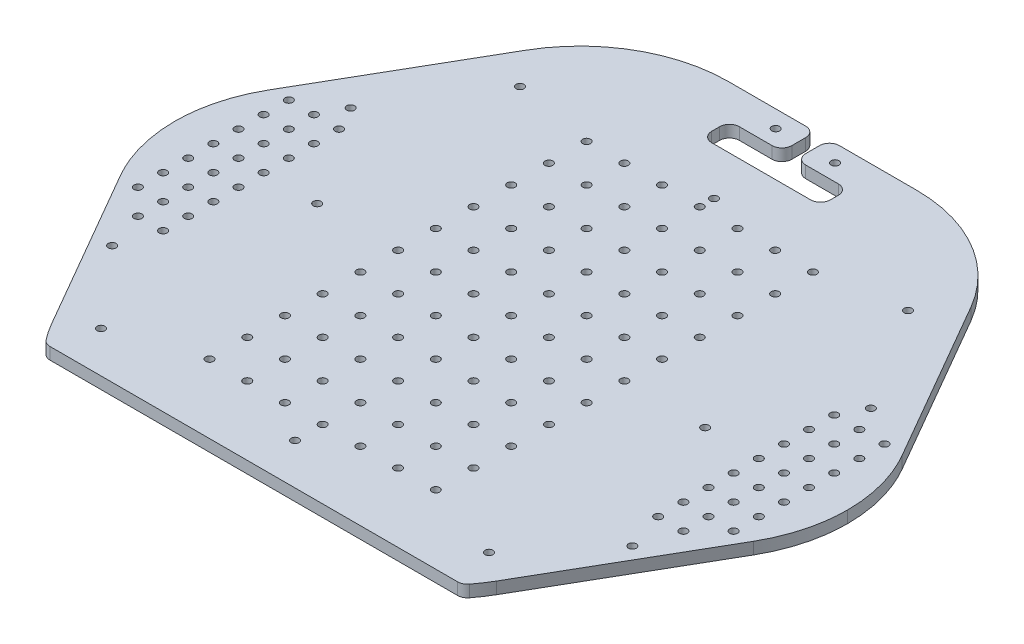
SolidWorks part; units mm, degrees
ref_plane "Front Plane" through (0, 0, 0) normal (0, 0, 1) x (1, 0, 0)
ref_plane "Top Plane" through (0, 0, 0) normal (0, 1, 0) x (1, 0, 0)
ref_plane "Right Plane" through (0, 0, 0) normal (1, 0, 0) x (0, 0, -1)
ref_plane "Plane1" through (0, 6, 0) normal (0, 1, 0) x (1, 0, 0)
sketch "Sketch1" plane through (0, 6, 0) normal (0, 1, 0) x (1, 0, 0)
  line L0 (112.4519, -119.7724) -> (159.9519, -37.5)
  line L1 (159.9519, 37.5) -> (90.8013, 157.2724)
  line L2 (90.8013, 157.2724) -> (-90.8013, 157.2724)
  line L3 (-90.8013, 157.2724) -> (-159.9519, 37.5)
  line L4 (-159.9519, -37.5) -> (-112.4519, -119.7724)
  line L5 (-105.3856, -130) -> (105.3856, -130)
  spline S0 degree 3 poles (105.3856, -130) (105.779, -129.4973) (106.1723, -128.9946) (106.5657, -128.4919) (108.7286, -125.7279) (110.697, -122.8118) (112.4519, -119.7724) knots 2.452075 2.452075 2.452075 2.452075 2.477608 2.477608 2.477608 2.617994 2.617994 2.617994 2.617994
  spline S1 degree 3 poles (159.9519, -37.5) (162.0898, -33.7968) (165.8426, -25.7861) (169.2445, -13.0899) (169.9999, -4.2761) (170, 0) knots 2.617994 2.617994 2.617994 2.617994 2.789036 2.97055 3.141593 3.141593 3.141593 3.141593
  spline S2 degree 3 poles (170, 0) (169.9999, 4.276) (169.2445, 13.0899) (165.8426, 25.7861) (162.0898, 33.7968) (159.9519, 37.5) knots 3.141593 3.141593 3.141593 3.141593 3.312635 3.494149 3.665191 3.665191 3.665191 3.665191
  spline S3 degree 3 poles (-159.9519, 37.5) (-162.0898, 33.7968) (-165.8426, 25.7861) (-169.2445, 13.0899) (-169.9999, 4.2761) (-170, 0) knots 5.759587 5.759587 5.759587 5.759587 5.930629 6.112143 6.283185 6.283185 6.283185 6.283185
  spline S4 degree 3 poles (-170, 0) (-169.9999, -4.2761) (-169.2445, -13.0899) (-165.8426, -25.7861) (-162.0898, -33.7968) (-159.9519, -37.5) knots 6.283185 6.283185 6.283185 6.283185 6.454228 6.635742 6.806784 6.806784 6.806784 6.806784
  spline S5 degree 3 poles (-112.4519, -119.7724) (-110.697, -122.8118) (-108.7286, -125.7279) (-106.5657, -128.4919) (-106.1723, -128.9946) (-105.779, -129.4973) (-105.3856, -130) knots 0.523599 0.523599 0.523599 0.523599 0.663985 0.663985 0.663985 0.689517 0.689517 0.689517 0.689517
extrude "Boss-Extrude1" add sketch "Sketch1" against normal blind 6
sketch "Sketch2" plane through (0, 0, 0) normal (0, -1, 0) x (1, 0, 0)
  line L0 (3.5, -157.2724) -> (3.5, -140.2724)
  line L1 (3.5, -140.2724) -> (30, -140.2724)
  line L2 (30, -140.2724) -> (30, -126.2724)
  line L3 (30, -126.2724) -> (-30, -126.2724)
  line L4 (-30, -126.2724) -> (-30, -140.2724)
  line L5 (-30, -140.2724) -> (-3.5, -140.2724)
  line L6 (-3.5, -140.2724) -> (-3.5, -157.2724)
  line L7 (-3.5, -157.2724) -> (3.5, -157.2724)
extrude "Cut-Extrude1" cut sketch "Sketch2" against normal through all
hole_wizard "M3.5 Clearance Hole1" positions "Sketch4" profile "Sketch3" hole size "M3.5" standard "ANSI Metric"
sketch "Sketch4" plane through (0, 6, 0) normal (0, 1, 0) x (1, 0, 0)
  point P0 (-150.4696, 38.1)
  point P1 (-150.4696, 25.4)
  point P2 (-150.4696, 12.7)
  point P3 (-150.4696, 0)
  point P4 (-150.4696, -12.7)
  point P5 (-150.4696, -25.4)
  point P6 (-150.4696, -38.1)
  point P7 (150.4696, -38.1)
  point P8 (150.4696, -25.4)
  point P9 (150.4696, -12.7)
  point P10 (150.4696, 0)
  point P11 (150.4696, 12.7)
  point P12 (150.4696, 25.4)
  point P13 (150.4696, 38.1)
sketch "Sketch3" plane through (-150.4696, 6, -38.1) normal (1, 0, 0) x (0, 0, 1)
  line L0 (0, 0) -> (0, 6.0001)
  line L1 (0, 6.0001) -> (1.9748, 6.0001)
  line L2 (1.9748, 6.0001) -> (1.9748, 0)
  line L5 (1.9748, 0) -> (0, 0)
  line L11 (0, -6.35) -> (0, 107.95) construction
  dimension "Thru Hole Dia." = 3.9496
  dimension "Thru Hole Depth" = 6.0001
hole_wizard "M3.5 Clearance Hole2" positions "Sketch6" profile "Sketch5" hole size "M3.5" standard "ANSI Metric"
sketch "Sketch6" plane through (0, 0, 0) normal (0, -1, 0) x (-1, 0, 0)
  point P0 (98, -109.22)
  point P1 (-98, 102.4382)
  point P2 (98, 102.4382)
  point P3 (0, 102.4382)
  point P4 (0, -109.22)
  point P5 (0, 0)
  point P6 (-19.05, 0)
  point P7 (-19.05, 19.05)
  point P8 (0, 19.05)
  point P9 (19.05, 19.05)
  point P10 (19.05, 0)
  point P11 (19.05, -19.05)
  point P12 (0, -19.05)
  point P13 (-19.05, -19.05)
  point P14 (-38.1, -19.05)
  point P15 (-38.1, 0)
  point P16 (-38.1, 19.05)
  point P17 (-38.1, 38.1)
  point P18 (-19.05, 38.1)
  point P19 (0, 38.1)
  point P20 (19.05, 38.1)
  point P21 (38.1, 38.1)
  point P22 (38.1, 19.05)
  point P23 (38.1, 0)
  point P24 (38.1, -19.05)
  point P25 (38.1, -38.1)
  point P26 (19.05, -38.1)
  point P27 (0, -38.1)
  point P28 (-19.05, -38.1)
  point P29 (-38.1, -38.1)
  point P30 (-57.15, -38.1)
  point P31 (-57.15, -19.05)
  point P32 (-57.15, 0)
  point P33 (-57.15, 19.05)
  point P34 (-57.15, 38.1)
  point P35 (-57.15, 57.15)
  point P36 (-38.1, 57.15)
  point P37 (-19.05, 57.15)
  point P38 (0, 57.15)
  point P39 (19.05, 57.15)
  point P40 (38.1, 57.15)
  point P41 (57.15, 57.15)
  point P42 (57.15, 38.1)
  point P43 (57.15, 19.05)
  point P44 (57.15, 0)
  point P45 (57.15, -19.05)
  point P46 (57.15, -38.1)
  point P47 (57.15, -57.15)
  point P48 (38.1, -57.15)
  point P49 (19.05, -57.15)
  point P50 (0, -57.15)
  point P51 (-19.05, -57.15)
  point P52 (-38.1, -57.15)
  point P53 (-57.15, -57.15)
  point P54 (-57.15, 76.2)
  point P55 (-38.1, 76.2)
  point P56 (-19.05, 76.2)
  point P57 (0, 76.2)
  point P58 (19.05, 76.2)
  point P59 (38.1, 76.2)
  point P60 (57.15, 76.2)
  point P61 (57.15, -76.2)
  point P62 (38.1, -76.2)
  point P63 (19.05, -76.2)
  point P64 (0, -76.2)
  point P65 (-19.05, -76.2)
  point P66 (-38.1, -76.2)
  point P67 (-57.15, -76.2)
  point P68 (-57.15, 95.25)
  point P69 (-38.1, 95.25)
  point P70 (-19.05, 95.25)
  point P71 (0, 95.25)
  point P72 (19.05, 95.25)
  point P73 (38.1, 95.25)
  point P74 (57.15, 95.25)
  point P75 (57.15, -95.25)
  point P76 (38.1, -95.25)
  point P77 (19.05, -95.25)
  point P78 (0, -95.25)
  point P79 (-19.05, -95.25)
  point P80 (-38.1, -95.25)
  point P81 (-57.15, -95.25)
  point P82 (-97.9932, 0)
  point P83 (-125.0696, 0)
  point P84 (-137.7696, 0)
  point P85 (-125.0696, -12.7)
  point P86 (-125.0696, -25.4)
  point P87 (-125.0696, -38.1)
  point P88 (-137.7696, -38.1)
  point P89 (-137.7696, -25.4)
  point P90 (-137.7696, -12.7)
  point P91 (-125.0696, 12.7)
  point P92 (-125.0696, 25.4)
  point P93 (-125.0696, 38.1)
  point P94 (-137.7696, 38.1)
  point P95 (-137.7696, 25.4)
  point P96 (-137.7696, 12.7)
  point P97 (97.9932, 0)
  point P98 (125.0696, 0)
  point P99 (137.7696, 0)
  point P100 (125.0696, -12.7)
  point P101 (125.0696, -25.4)
  point P102 (125.0696, -38.1)
  point P103 (137.7696, -38.1)
  point P104 (137.7696, -25.4)
  point P105 (137.7696, -12.7)
  point P106 (125.0696, 12.7)
  point P107 (125.0696, 25.4)
  point P108 (125.0696, 38.1)
  point P109 (137.7696, 38.1)
  point P110 (137.7696, 25.4)
  point P111 (137.7696, 12.7)
  point P112 (-137.7696, -50.8)
  point P113 (-125.0696, -50.8)
  point P114 (137.7696, -50.8)
  point P115 (125.0696, -50.8)
  point P116 (-98, -109.22)
  point P117 (131.4, 50.3)
  point P118 (-131.4, 50.3)
  point P119 (131.4, -70.2)
  point P120 (-131.4, -70.2)
  point P121 (15, 148.6)
  point P122 (-15, 148.6)
sketch "Sketch5" plane through (-98, 0, 109.22) normal (1, 0, 0) x (0, 0, -1)
  line L0 (0, 0) -> (0, 6.0001)
  line L1 (0, 6.0001) -> (1.9748, 6.0001)
  line L2 (1.9748, 6.0001) -> (1.9748, 0)
  line L5 (1.9748, 0) -> (0, 0)
  line L11 (0, -6.35) -> (0, 107.95) construction
  dimension "Thru Hole Dia." = 3.9496
  dimension "Thru Hole Depth" = 6.0001
fillet "Fillet1" radius 5.0207 10 edges at (-105.3856, 3, 130) (3.5, 3, -140.2724) (-30, 3, -126.2724) (-30, 3, -140.2724) (-3.5, 3, -140.2724) (30, 3, -140.2724) (105.3856, 3, 130) (30, 3, -126.2724)
fillet "Fillet2" radius 74.9585 2 edges at (90.8013, 3, -157.2724) (-90.8013, 3, -157.2724)
